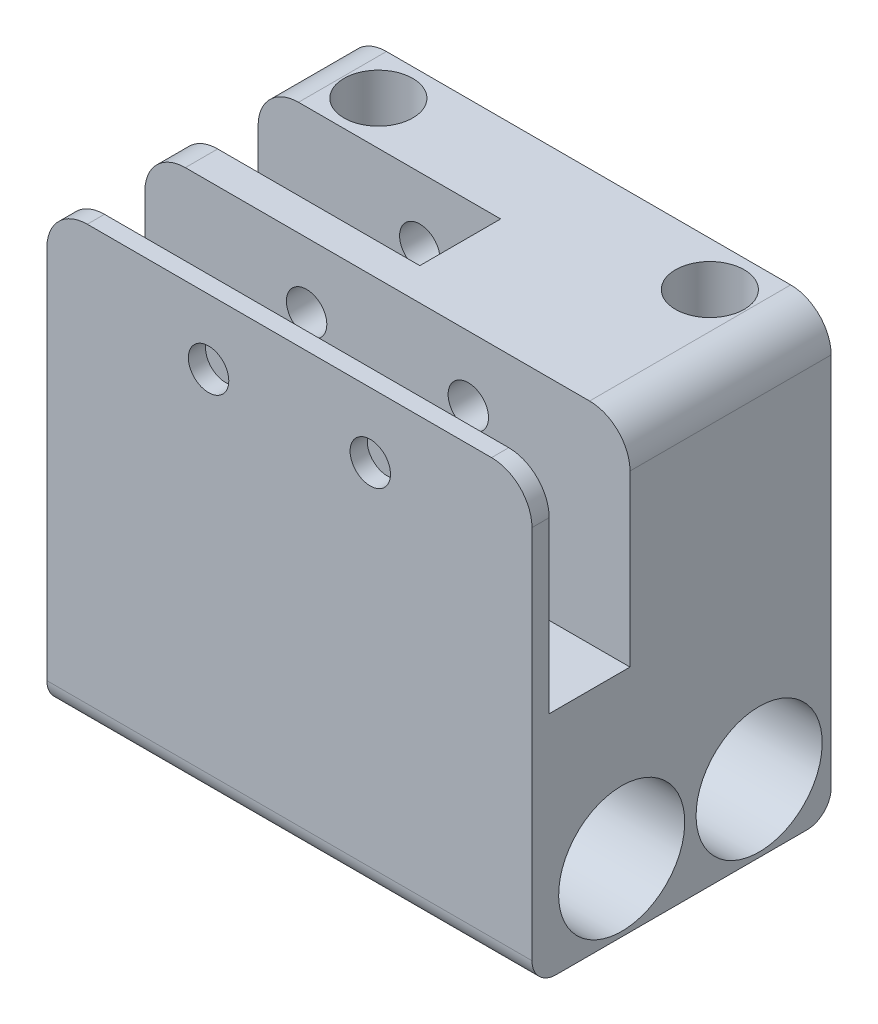
SolidWorks part; units mm, degrees
ref_plane "Front Plane" through (0, 0, 0) normal (0, 0, 1) x (1, 0, 0)
ref_plane "Top Plane" through (0, 0, 0) normal (0, 1, 0) x (1, 0, 0)
ref_plane "Right Plane" through (0, 0, 0) normal (1, 0, 0) x (0, 0, -1)
sketch "Esboço2" plane through (0, 0, 0) normal (0, 0, 1) x (1, 0, 0)
  line L7 (-246.2188, 113.8225) -> (-237.7812, 113.8225)
  line L8 (-201.9668, 113.8225) -> (-194.0332, 113.8225)
  line L9 (-250, 138.1236) -> (-250, 163.2122)
  line L10 (-245, 168.2122) -> (-195, 168.2122)
  line L11 (-190, 163.2122) -> (-190, 138.1236)
  line L21 (-194.0332, 113.8225) -> (-190, 113.8225)
  line L22 (-190, 113.8225) -> (-190, 138.1236)
  line L25 (-250, 138.1236) -> (-250, 113.8225)
  line L26 (-250, 113.8225) -> (-246.2188, 113.8225)
  line L27 (-237.7812, 113.8225) -> (-201.9668, 113.8225)
  arc A5 (-195, 168.2122) -> (-190, 163.2122) centre (-195, 163.2122) cw
  arc A6 (-250, 163.2122) -> (-245, 168.2122) centre (-245, 163.2122) cw
  point P8 (-190, 168.2122)
  point P11 (-250, 168.2122)
  dimension "D1" = 5
extrude "Ressalto-extrusão1" add sketch "Esboço2" along normal up to vertex (40 mm away)
sketch "Esboço4" plane through (-190, 0, 0) normal (1, 0, 0) x (0, 0, -1)
  circle A2 centre (-11.9024, 122.2122) radius 7.8
  circle A3 centre (-11.9024, 122.2122) radius 7.8
  circle A5 centre (-28.9024, 122.2122) radius 7.8
  circle A6 centre (-28.9024, 122.2122) radius 7.8
  dimension "D1" = 0.3
  dimension "D2" = 0.3
extrude "Corte-extrusão1" cut sketch "Esboço4" against normal through all
sketch "Esboço5" plane through (0, 0, 0) normal (0, 0, -1) x (-1, 0, 0)
  line L8 (190, 163.2122) -> (190, 113.8225)
  line L9 (190, 113.8225) -> (250, 113.8225)
  line L10 (250, 113.8225) -> (250, 163.2122)
  line L11 (245, 168.2122) -> (195, 168.2122)
  line L12 (190, 163.2122) -> (190, 113.8225)
  line L13 (190, 113.8225) -> (250, 113.8225)
  line L14 (250, 113.8225) -> (250, 163.2122)
  line L15 (245, 168.2122) -> (195, 168.2122)
  arc A4 (195, 168.2122) -> (190, 163.2122) centre (195, 163.2122) ccw
  arc A5 (250, 163.2122) -> (245, 168.2122) centre (245, 163.2122) ccw
  arc A6 (195, 168.2122) -> (190, 163.2122) centre (195, 163.2122) ccw
  arc A7 (250, 163.2122) -> (245, 168.2122) centre (245, 163.2122) ccw
  dimension "D1" = 0
extrude "Corte-extrusão2" cut sketch "Esboço5" against normal blind 3
fillet "Filete2" radius 3 2 edges at (-220, 113.8225, 3) (-220, 113.8225, 40)
sketch "Esboço7" plane through (-190, 0, 0) normal (1, 0, 0) x (0, 0, -1)
  line L3 (-37.8749, 142.2122) -> (-37.8749, 152.2122) construction
  line L4 (-27.8749, 142.2122) -> (-27.8749, 152.2122) construction
  line L5 (-27.8749, 142.2122) -> (-37.8749, 142.2122) construction
  line L6 (-37.8749, 142.2122) -> (-37.8749, 152.2122)
  line L7 (-27.8749, 142.2122) -> (-27.8749, 152.2122)
  line L8 (-27.8749, 142.2122) -> (-37.8749, 142.2122)
  line L9 (-27.8749, 152.2122) -> (-27.8749, 170.6394)
  line L10 (-37.8749, 152.2122) -> (-37.8749, 170.6394)
  line L11 (-37.8749, 170.6394) -> (-27.8749, 170.6394)
extrude "Corte-extrusão4" cut sketch "Esboço7" against normal through all
sketch "Esboço8" plane through (-250, 0, 0) normal (-1, 0, 0) x (0, 0, 1)
  line L0 (23.8749, 142.2122) -> (23.8749, 152.2122) construction
  line L1 (13.8749, 142.2122) -> (23.8749, 142.2122) construction
  line L2 (13.8749, 142.2122) -> (13.8749, 152.2122) construction
  line L3 (23.8749, 142.2122) -> (23.8749, 152.2122)
  line L4 (13.8749, 142.2122) -> (23.8749, 142.2122)
  line L5 (13.8749, 142.2122) -> (13.8749, 152.2122)
  line L6 (23.8749, 152.2122) -> (23.8749, 182.1915)
  line L7 (23.8749, 182.1915) -> (13.8749, 182.1915)
  line L8 (13.8749, 182.1915) -> (13.8749, 152.2122)
sketch "Esboço9" plane through (0, 168.2122, 0) normal (0, 1, 0) x (1, 0, 0)
  line L0 (-220, -40) -> (-220, -3) construction
  line L1 (-195, -40) -> (-245, -40) construction
  line L2 (-245, -3) -> (-195, -3) construction
extrude "Corte-extrusão5" cut sketch "Esboço8" against normal up to vertex (30 mm away) up to point (-220, 168.2122, 40)
sketch "Esboço10" plane through (0, 0, 40) normal (0, 0, 1) x (1, 0, 0)
  line L0 (-739.8206, 160.1731) -> (-189.8206, 160.1731) construction
  line L1 (-190, 116.8225) -> (-190, 163.2122) construction
  line L2 (-250, 163.2122) -> (-250, 116.8225) construction
  circle A0 centre (-210, 160.1731) radius 2.5
  circle A2 centre (-230, 160.1731) radius 2.5
  dimension "D1" = 5
  dimension "D2" = 20
  dimension "D3" = 20
extrude "Corte-extrusão6" cut sketch "Esboço10" against normal through all
sketch "Esboço11" plane through (0, 168.2122, 0) normal (0, 1, 0) x (1, 0, 0)
  line L2 (-190, -27.8749) -> (-190, -3) construction
  line L3 (-245, -3) -> (-195, -3) construction
  line L4 (-220, -40) -> (-220, -3) construction
  line L5 (-195, -40) -> (-245, -40) construction
  circle A0 centre (-199.5, -8.5) radius 4.25
  circle A2 centre (-240.5, -8.5) radius 4.25
  dimension "D1" = 8.5
  dimension "D2" = 9.5
  dimension "D3" = 5.5
extrude "Corte-extrusão7" cut sketch "Esboço11" against normal blind 30
